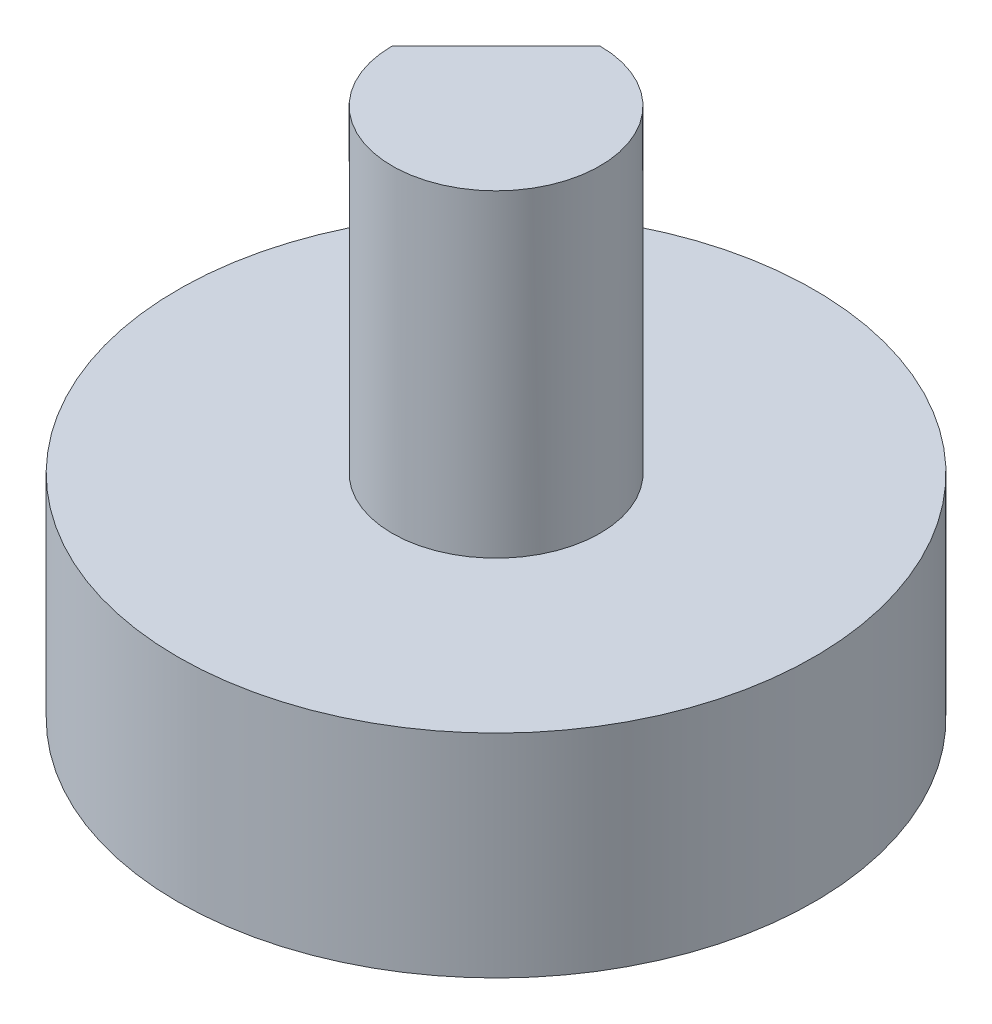
SolidWorks part; units mm, degrees
ref_plane "Front Plane" through (0, 0, 0) normal (0, 0, 1) x (1, 0, 0)
ref_plane "Top Plane" through (0, 0, 0) normal (0, 1, 0) x (1, 0, 0)
ref_plane "Right Plane" through (0, 0, 0) normal (1, 0, 0) x (0, 0, -1)
sketch "Sketch1" plane through (0, 0, 0) normal (0, 1, 0) x (1, 0, 0)
  circle A0 centre (0, 0) radius 15
extrude "Boss-Extrude1" add sketch "Sketch1" along normal blind 10
sketch "Sketch2" plane through (0, 10, 0) normal (0, 1, 0) x (1, 0, 0)
  circle A0 centre (0, 0) radius 4.9
  dimension "D1" = 9.8
extrude "Boss-Extrude2" add sketch "Sketch2" along normal blind 15
sketch "Sketch3" plane through (0, 25, 0) normal (0, 1, 0) x (1, 0, 0)
  line L0 (-4.9, 0) -> (0, 4.9)
  arc A0 (0, 4.9) -> (-4.9, 0) centre (0, 0) ccw
extrude "Cut-Extrude1" cut sketch "Sketch3" against normal blind 4
